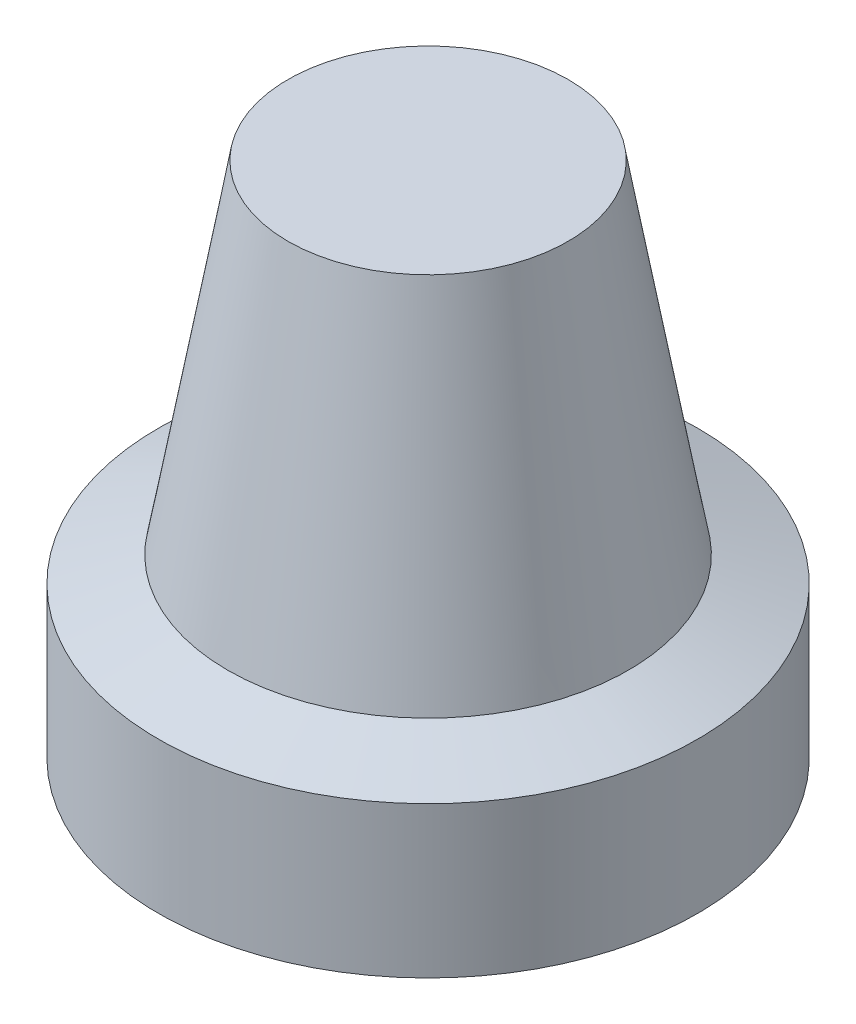
SolidWorks part; units mm, degrees
ref_plane "Front" through (0, 0, 0) normal (0, 0, 1) x (1, 0, 0)
ref_plane "Top" through (0, 0, 0) normal (0, 1, 0) x (1, 0, 0)
ref_plane "Right" through (0, 0, 0) normal (1, 0, 0) x (0, 0, -1)
other "Bounding Box"
ref_plane "Default Plane" through (-37.2876, 0, 53.2522) normal (-0.1736, 0, -0.9848) x (-0.9848, 0, 0.1736)
sketch "Sketch2" plane through (0, 0, 0) normal (0, 0, 1) x (1, 0, 0)
  line L0 (0, -4.502) -> (0, 25.0378) construction
  line L1 (0, 0) -> (5, 0)
  line L2 (5, 0) -> (10.5, -2)
  line L3 (10.5, -2) -> (12.5, -2)
  line L4 (12.5, -2) -> (12.5, 5)
  line L5 (12.5, 5) -> (9.2917, 6.1677)
  line L6 (9.2917, 6.1677) -> (6.5, 22)
  line L7 (6.5, 22) -> (0, 22)
  line L8 (0, 0) -> (0, 22)
  dimension "D1" = 12.5
  dimension "D2" = 2
  dimension "D3" = 5
  dimension "D4" = 2
  dimension "D5" = 6.5
  dimension "D6" = 110
  dimension "D7" = 100
  dimension "D8" = 22
  dimension "D9" = 7
revolve "Revolve1" add sketch "Sketch2" angle 360 about L0
sketch "Sketch3" plane through (0, 0, 0) normal (0, -1, 0) x (1, 0, 0)
  circle A0 centre (0, 0) radius 3
  dimension "D1" = 6
extrude "Cut-Extrude1" cut sketch "Sketch3" against normal blind 10
